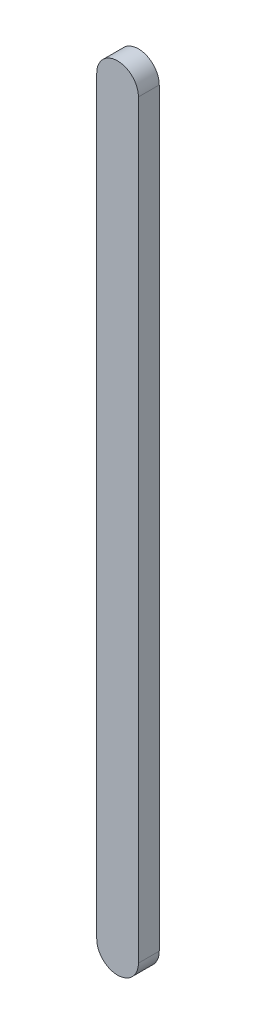
SolidWorks part; units mm, degrees
ref_plane "前视基准面" through (0, 0, 0) normal (0, 0, 1) x (1, 0, 0)
ref_plane "上视基准面" through (0, 0, 0) normal (0, 1, 0) x (1, 0, 0)
ref_plane "右视基准面" through (0, 0, 0) normal (1, 0, 0) x (0, 0, -1)
sketch "草图1" plane through (0, 0, 0) normal (0, 0, 1) x (1, 0, 0)
  line L0 (0, 0) -> (0, -180) construction
  line L1 (5, 0) -> (5, -180)
  line L2 (-5, 0) -> (-5, -180)
  arc A0 (5, 0) -> (-5, 0) centre (0, 0) ccw
  arc A1 (-5, -180) -> (5, -180) centre (0, -180) ccw
  point P3 (0, -90)
extrude "凸台-拉伸1" add sketch "草图1" along normal blind 5
